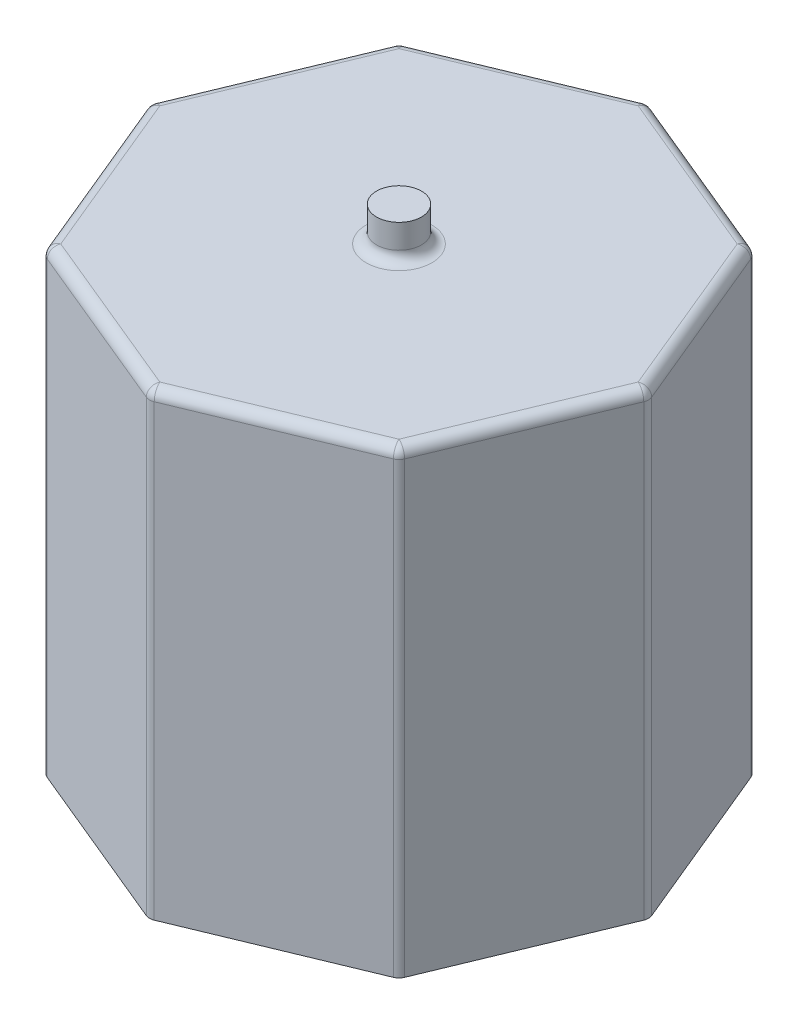
SolidWorks part; units mm, degrees
material "ABS"
ref_plane "Front Plane" through (0, 0, 0) normal (0, 0, 1) x (1, 0, 0)
ref_plane "Top Plane" through (0, 0, 0) normal (0, 1, 0) x (1, 0, 0)
ref_plane "Right Plane" through (0, 0, 0) normal (1, 0, 0) x (0, 0, -1)
sketch "Sketch1" plane through (0, 0, 0) normal (0, 1, 0) x (1, 0, 0)
  line L1 (7.25, 0) -> (5.1265, 5.1265)
  line L2 (5.1265, 5.1265) -> (0, 7.25)
  line L3 (0, 7.25) -> (-5.1265, 5.1265)
  line L4 (-5.1265, 5.1265) -> (-7.25, 0)
  line L5 (-7.25, 0) -> (-5.1265, -5.1265)
  line L6 (-5.1265, -5.1265) -> (0, -7.25)
  line L7 (0, -7.25) -> (5.1265, -5.1265)
  line L8 (5.1265, -5.1265) -> (7.25, 0)
  circle A0 centre (0, 0) radius 6.6981 construction
  dimension "D1" = 14.5
extrude "Boss-Extrude1" add sketch "Sketch1" along normal blind 13.3
sketch "Sketch2" plane through (0, 13.3, 0) normal (0, 1, 0) x (1, 0, 0)
  circle A0 centre (0, 0) radius 0.65
  dimension "D1" = 1.3
extrude "Boss-Extrude2" add sketch "Sketch2" along normal blind 1
fillet "Fillet1" radius 0.3 8 edges at (-5.1265, 6.65, 5.1265) (-7.25, 6.65, 0) (-5.1265, 6.65, -5.1265) (0, 6.65, -7.25) (5.1265, 6.65, -5.1265) (7.25, 6.65, 0) (5.1265, 6.65, 5.1265) (0, 6.65, 7.25)
fillet "Fillet2" radius 0.3 17 edges at (7.2253, 13.3, 0) (6.1883, 13.3, 2.5633) (5.109, 13.3, 5.109) (2.5633, 13.3, 6.1883) (0, 13.3, 7.2253) (-2.5633, 13.3, 6.1883) (-5.109, 13.3, 5.109) (-6.1883, 13.3, 2.5633) (-7.2253, 13.3, 0) (-6.1883, 13.3, -2.5633) (-5.109, 13.3, -5.109) (-2.5633, 13.3, -6.1883) (0, 13.3, -7.2253) (2.5633, 13.3, -6.1883) (5.109, 13.3, -5.109) (6.1883, 13.3, -2.5633) (0, 13.3, 0.65)
